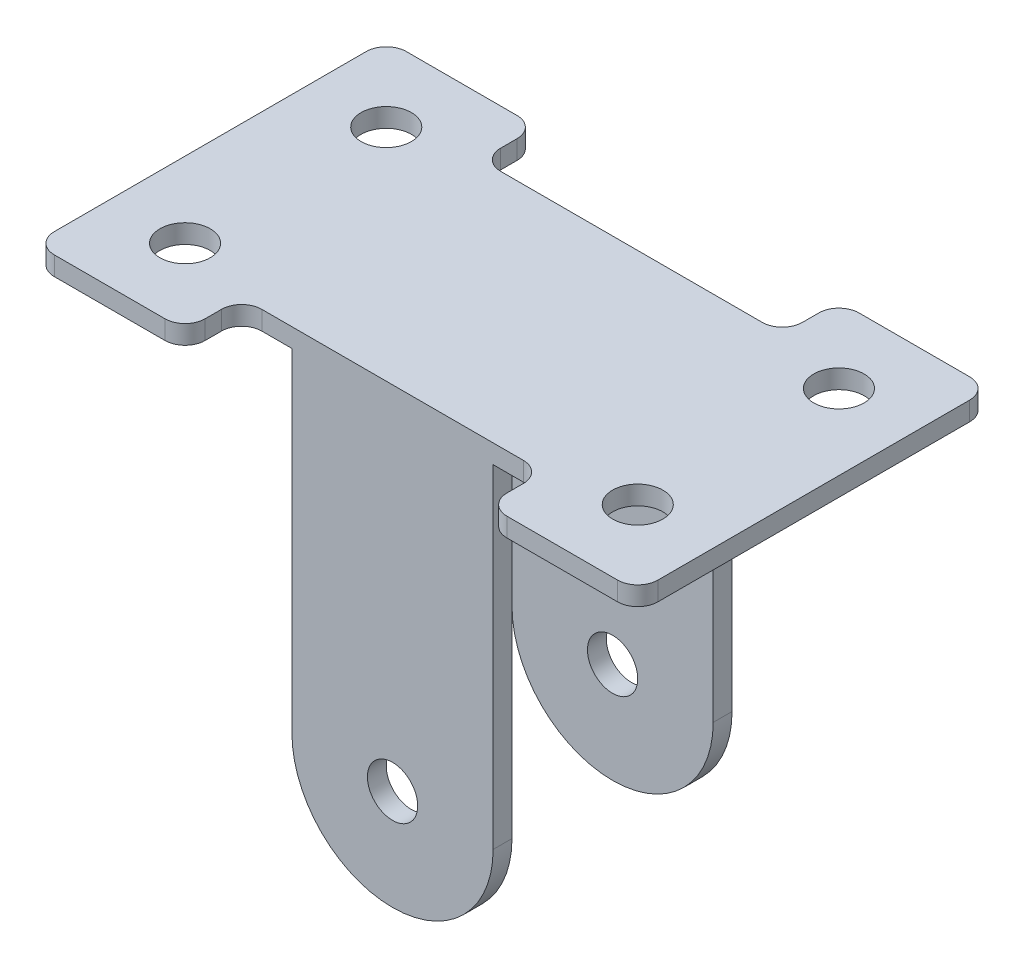
SolidWorks part; units mm, degrees
ref_plane "Front Plane" through (0, 0, 0) normal (0, 0, 1) x (1, 0, 0)
ref_plane "Top Plane" through (0, 0, 0) normal (0, 1, 0) x (1, 0, 0)
ref_plane "Right Plane" through (0, 0, 0) normal (1, 0, 0) x (0, 0, -1)
sketch "Sketch1" plane through (0, 0, 0) normal (0, 1, 0) x (1, 0, 0)
  line L1 (-38.1, 22.225) -> (38.1, 22.225)
  line L2 (-38.1, 22.225) -> (-38.1, -22.225)
  line L3 (-38.1, -22.225) -> (38.1, -22.225)
  line L4 (38.1, 22.225) -> (38.1, -22.225)
  dimension "D1" = 76.2
  dimension "D2" = 44.45
  dimension "D3" = 38.1
  dimension "D4" = 22.225
extrude "Boss-Extrude1" add sketch "Sketch1" along normal blind 2.3813
sketch "Sketch2" plane through (0, 2.3813, 0) normal (0, 1, 0) x (1, 0, 0)
  line L0 (-38.1, -22.225) -> (38.1, -22.225) construction
  line L1 (-38.1, 22.225) -> (-38.1, -22.225) construction
  circle A0 centre (-28.575, -12.7) radius 3.175
  circle A1 centre (-28.575, 12.7) radius 3.175
  circle A2 centre (28.575, 12.7) radius 3.175
  circle A3 centre (28.575, -12.7) radius 3.175
  dimension "D1" = 25.4
  dimension "D3" = 57.15
  dimension "D4" = 57.15
  dimension "D6" = 9.525
  dimension "D7" = 6.35
  dimension "D2" = 25.4
  dimension "D5" = 9.525
extrude "Cut-Extrude1" cut sketch "Sketch2" against normal blind 2.3813
sketch "Sketch5" plane through (0, 2.3813, 0) normal (0, 1, 0) x (1, 0, 0)
  line L0 (-38.1, -22.225) -> (38.1, -22.225) construction
  line L1 (-19.05, -22.225) -> (19.05, -22.225)
  line L2 (-19.05, -22.225) -> (-19.05, -15.0812)
  line L3 (-19.05, -15.0812) -> (19.05, -15.0812)
  line L4 (19.05, -22.225) -> (19.05, -15.0812)
  line L5 (38.1, -22.225) -> (38.1, 22.225) construction
  line L6 (-38.1, 22.225) -> (-38.1, -22.225) construction
  dimension "D1" = 7.1437
  dimension "D2" = 19.05
  dimension "D3" = 19.05
extrude "Cut-Extrude4" cut sketch "Sketch5" against normal blind 2.3813
sketch "Sketch6" plane through (0, 0, 15.0812) normal (0, 0, 1) x (1, 0, 0)
  line L0 (19.05, 0) -> (-19.05, 0) construction
  line L1 (-12.7, 2.3813) -> (12.7, 2.3813)
  line L2 (-12.7, 2.3813) -> (-12.7, -42.0687)
  line L4 (12.7, 2.3813) -> (12.7, -42.0687)
  arc A0 (-12.7, -42.0687) -> (12.7, -42.0687) centre (0, -42.0687) ccw
  dimension "D1" = 25.4
  dimension "D2" = 44.45
  dimension "D3" = 12.7
  dimension "D4" = 2.3813
extrude "Boss-Extrude4" add sketch "Sketch6" against normal blind 2.3813
sketch "Sketch7" plane through (0, 0, 15.0812) normal (0, 0, 1) x (1, 0, 0)
  line L0 (-12.7, 0) -> (-12.7, -42.0687) construction
  circle A0 centre (0, -42.0687) radius 3.175
  dimension "D1" = 6.35
  dimension "D3" = 12.7
  dimension "D2" = 0
extrude "Cut-Extrude5" cut sketch "Sketch7" against normal blind 2.3813
mirror "Mirror2" about plane through (0, 0, 0) normal (0, 0, 1) of "Boss-Extrude4", "Cut-Extrude4", "Cut-Extrude5"
fillet "Fillet1" radius 2.54 12 edges at (38.1, 1.1906, 22.225) (19.05, 1.1906, -15.0812) (38.1, 1.1906, -22.225) (19.05, 1.1906, -22.225) (-19.05, 1.1906, -15.0812) (-19.05, 1.1906, -22.225) (-38.1, 1.1906, 22.225) (-38.1, 1.1906, -22.225) (19.05, 1.1906, 22.225) (19.05, 1.1906, 15.0812) (-19.05, 1.1906, 22.225) (-19.05, 1.1906, 15.0812)
